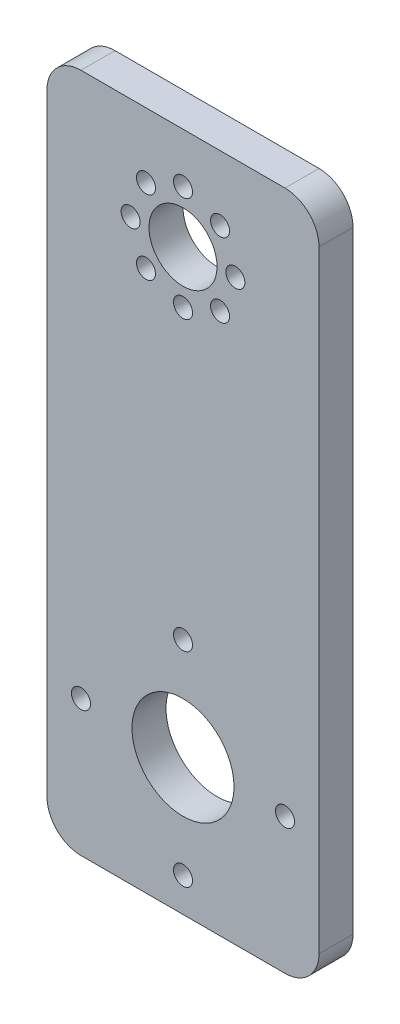
SolidWorks part; units mm, degrees
material "6061-T6 (SS)"
ref_plane "Front Plane" through (0, 0, 0) normal (0, 0, 1) x (1, 0, 0)
ref_plane "Top Plane" through (0, 0, 0) normal (0, 1, 0) x (1, 0, 0)
ref_plane "Right Plane" through (0, 0, 0) normal (1, 0, 0) x (0, 0, -1)
sketch "Sketch1" plane through (0, 0, 0) normal (0, 0, 1) x (1, 0, 0)
  line L1 (0, 0) -> (50.8, 0)
  line L2 (0, 0) -> (0, 127)
  line L3 (0, 127) -> (50.8, 127)
  line L4 (50.8, 0) -> (50.8, 127)
  circle A0 centre (25.4, 25.4) radius 9.525
  circle A5 centre (25.4, 107.95) radius 6.35
  dimension "D1" = 50.8
  dimension "D3" = 19.05
  dimension "D6" = 12.7
  dimension "D2" = 127
  dimension "D4" = 25.4
  dimension "D5" = 101.6
  dimension "D7" = 19.05
  dimension "D8" = 25.4
extrude "Boss-Extrude1" add sketch "Sketch1" along normal blind 6.35
sketch "Sketch2" plane through (0, 0, 6.35) normal (0, 0, 1) x (1, 0, 0)
  line L0 (50.8, 0) -> (50.8, 127) construction
  circle A0 centre (25.4, 44.45) radius 1.778
  circle A1 centre (25.4, 25.4) radius 9.525 construction
  dimension "D1" = 19.05
  dimension "D2" = 3.556
  dimension "D3" = 25.4
extrude "Cut-Extrude1" cut sketch "Sketch2" against normal blind 6.35
pattern_circular "CirPattern1" count 4 over 360 about axis through (25.4, 25.4, 0) along (0, 0, 1) of "Cut-Extrude1"
sketch "Sketch3" plane through (0, 0, 6.35) normal (0, 0, 1) x (1, 0, 0)
  line L1 (50.8, 0) -> (50.8, 127) construction
  circle A0 centre (25.4, 117.729) radius 1.778
  circle A1 centre (25.4, 107.95) radius 6.35 construction
  dimension "D1" = 3.556
  dimension "D2" = 25.4
  dimension "D3" = 9.779
extrude "Cut-Extrude2" cut sketch "Sketch3" against normal blind 6.35
pattern_circular "CirPattern2" count 8 over 360 about axis through (25.4, 107.95, 0) along (0, 0, 1) of "Cut-Extrude2"
fillet "Fillet1" radius 6.35 4 edges at (0, 0, 3.175) (50.8, 0, 3.175) (0, 127, 3.175) (50.8, 127, 3.175)
